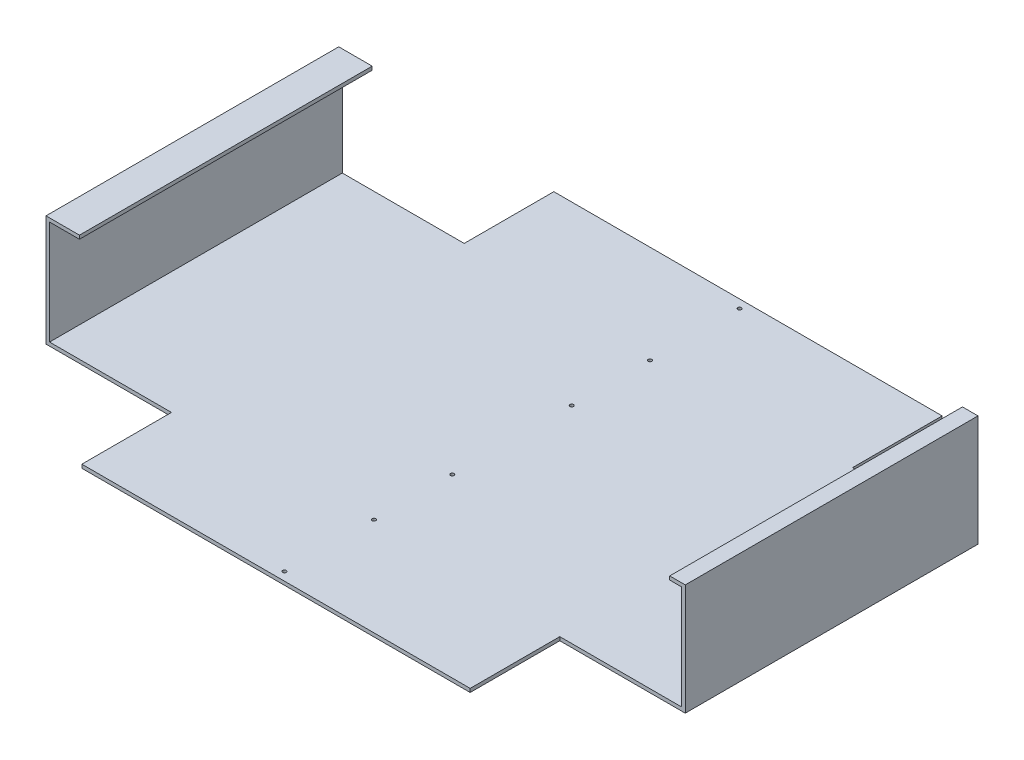
SolidWorks part; units mm, degrees
ref_plane "Front Plane" through (0, 0, 0) normal (0, 0, 1) x (1, 0, 0)
ref_plane "Top Plane" through (0, 0, 0) normal (0, 1, 0) x (1, 0, 0)
ref_plane "Right Plane" through (0, 0, 0) normal (1, 0, 0) x (0, 0, -1)
sketch "Sketch1" plane through (0, 0, 0) normal (0, 1, 0) x (1, 0, 0)
  line L1 (-267.5, -197.5) -> (267.5, -197.5)
  line L2 (-267.5, -197.5) -> (-267.5, 197.5)
  line L3 (-267.5, 197.5) -> (267.5, 197.5)
  line L4 (267.5, -197.5) -> (267.5, 197.5)
  line L5 (-267.5, -197.5) -> (267.5, 197.5) construction
  line L6 (-267.5, 197.5) -> (267.5, -197.5) construction
  point P0 (0, 0)
extrude "Boss-Extrude1" add sketch "Sketch1" along normal blind 3
sketch "Sketch2" plane through (0, 3, 0) normal (0, 1, 0) x (1, 0, 0)
  line L1 (-267.5, 197.5) -> (-162.5, 197.5)
  line L2 (-267.5, 197.5) -> (-267.5, 122.5)
  line L3 (-267.5, 122.5) -> (-162.5, 122.5)
  line L4 (-162.5, 197.5) -> (-162.5, 122.5)
extrude "Cut-Extrude1" cut sketch "Sketch2" against normal blind 3
mirror "Mirror1" about plane through (0, 0, 0) normal (0, 0, 1) of "Cut-Extrude1"
mirror "Mirror2" about plane through (0, 0, 0) normal (1, 0, 0) of "Cut-Extrude1", "Mirror1"
sketch "Sketch3" plane through (0, 3, 0) normal (0, 1, 0) x (1, 0, 0)
  line L0 (-267.5, -122.5) -> (-162.5, -122.5) construction
  line L1 (-267.5, 122.5) -> (-264.5, 122.5)
  line L2 (-267.5, 122.5) -> (-267.5, -122.5)
  line L3 (-267.5, -122.5) -> (-264.5, -122.5)
  line L4 (-264.5, 122.5) -> (-264.5, -122.5)
extrude "Boss-Extrude2" add sketch "Sketch3" along normal blind 90
sketch "Sketch4" plane through (-264.5, 0, 0) normal (1, 0, 0) x (0, 0, -1)
  line L0 (122.5, 93) -> (122.5, 3) construction
  line L1 (-122.5, 93) -> (122.5, 93)
  line L2 (-122.5, 93) -> (-122.5, 90)
  line L3 (-122.5, 90) -> (122.5, 90)
  line L4 (122.5, 93) -> (122.5, 90)
extrude "Boss-Extrude3" add sketch "Sketch4" along normal blind 25
sketch "Sketch5" plane through (0, 3, 0) normal (0, 1, 0) x (1, 0, 0)
  line L0 (267.5, -122.5) -> (162.5, -122.5) construction
  line L1 (267.5, 122.5) -> (264.5, 122.5)
  line L2 (267.5, 122.5) -> (267.5, -122.5)
  line L3 (267.5, -122.5) -> (264.5, -122.5)
  line L4 (264.5, 122.5) -> (264.5, -122.5)
extrude "Boss-Extrude4" add sketch "Sketch5" along normal blind 90
sketch "Sketch6" plane through (264.5, 0, 0) normal (-1, 0, 0) x (0, 0, 1)
  line L0 (122.5, 0) -> (122.5, 93) construction
  line L1 (-122.5, 93) -> (122.5, 93)
  line L2 (-122.5, 93) -> (-122.5, 90)
  line L3 (-122.5, 90) -> (122.5, 90)
  line L4 (122.5, 93) -> (122.5, 90)
extrude "Boss-Extrude5" add sketch "Sketch6" along normal blind 10
sketch "Sketch7" plane through (0, 3, 0) normal (0, 1, 0) x (1, 0, 0)
  circle A0 centre (0, 50) radius 1.5
  circle A1 centre (0, -50) radius 1.5
  dimension "D1" = 50
  dimension "D2" = 50
extrude "Cut-Extrude2" cut sketch "Sketch7" against normal blind 3
sketch "Sketch8" plane through (0, 3, 0) normal (0, 1, 0) x (1, 0, 0)
  line L0 (-162.5, -197.5) -> (162.5, -197.5) construction
  circle A0 centre (0, -190.5) radius 1.5
  dimension "D1" = 7
extrude "Cut-Extrude3" cut sketch "Sketch8" against normal through all
sketch "Sketch9" plane through (0, 3, 0) normal (0, 1, 0) x (1, 0, 0)
  line L0 (-264.5, -122.5) -> (-162.5, -122.5) construction
  circle A0 centre (0, -115.5) radius 1.5
  dimension "D1" = 7
extrude "Cut-Extrude4" cut sketch "Sketch9" against normal through all
mirror "Mirror3" about plane through (0, 0, 0) normal (0, 0, 1) of "Cut-Extrude4", "Cut-Extrude3"
